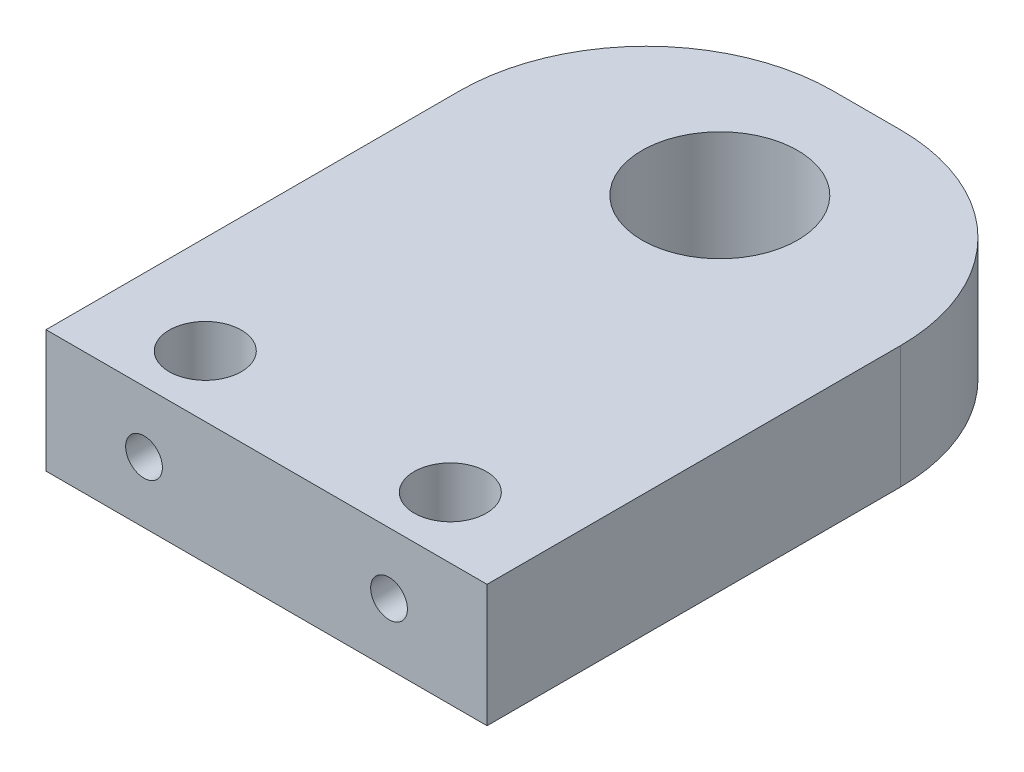
SolidWorks part; units mm, degrees
material "6061-T6 (SS)"
ref_plane "Front" through (0, 0, 0) normal (0, 0, 1) x (1, 0, 0)
ref_plane "Top" through (0, 0, 0) normal (0, 1, 0) x (1, 0, 0)
ref_plane "Right" through (0, 0, 0) normal (1, 0, 0) x (0, 0, -1)
sketch "Sketch1" plane through (0, 0, 0) normal (0, 1, 0) x (1, 0, 0)
  line L1 (0, 0) -> (-18, 0)
  line L2 (0, 0) -> (0, 24.5)
  line L3 (0, 24.5) -> (-18, 24.5)
  line L4 (-18, 0) -> (-18, 24.5)
  dimension "D1" = 18
  dimension "D2" = 24.5
extrude "Extrude1" add sketch "Sketch1" along normal blind 5
ref_plane "Plane1" through (-9, 0, 0) normal (1, 0, 0) x (0, 0, -1)
sketch "Sketch3" plane through (0, 5, 0) normal (0, 1, 0) x (1, 0, 0)
  line L0 (-18, 0) -> (0, 0) construction
  line L1 (-9, -2.75) -> (-9, 2.75) construction
  circle A0 centre (-14, 2.5) radius 1.4732
  dimension "D1" = 2.9464
  dimension "D2" = 2.5
  dimension "D3" = 5
extrude "Extrude2" cut sketch "Sketch3" against normal through all
sketch "Sketch4" plane through (0, 0, 0) normal (0, 0, 1) x (1, 0, 0)
  line L0 (-18, 0) -> (0, 0) construction
  line L1 (-9, -2.75) -> (-9, 2.75) construction
  circle A0 centre (-14, 2.5) radius 0.75
  dimension "D1" = 1.5
  dimension "D2" = 2.5
  dimension "D3" = 5
extrude "Extrude3" cut sketch "Sketch4" against normal blind 2.46
mirror "Mirror1" about plane through (-9, 0, 0) normal (1, 0, 0) of "Extrude2", "Extrude3"
fillet "Fillet1" radius 7.62 2 edges at (-18, 2.5, -24.5) (0, 2.5, -24.5)
hole_wizard "1/4-20 Tapped Hole1" positions "3DSketch1" profile "Sketch5" tap size "1/4-20" standard "Ansi Inch"
sketch3d "3DSketch1"
  line L1 (-18, 5, 0) -> (0, 5, 0) construction
  point P0 (-9, 5, -18.5)
  dimension "D1" = 18.5
sketch "Sketch5" plane through (-9, 5, -18.5) normal (1, 0, 0) x (0, 0, 1)
  line L0 (0, 0) -> (0, 18.0438)
  line L1 (0, 18.0438) -> (2.5527, 16.51)
  line L2 (2.5527, 16.51) -> (2.5527, 12.7)
  line L3 (2.5527, 12.7) -> (3.175, 12.7)
  line L4 (3.175, 12.7) -> (3.175, 0)
  line L5 (3.175, 0) -> (0, 0)
  line L10 (0, 18.0438) -> (-2.5527, 16.51) construction
  line L11 (0, -6.35) -> (0, 107.95) construction
  dimension "Tap Drill Dia." = 5.1054
  dimension "Tap Drill Depth" = 16.51
  dimension "Thread Major Dia." = 6.35
  dimension "Thread Depth" = 12.7
  dimension "Drill Angle" = 118
